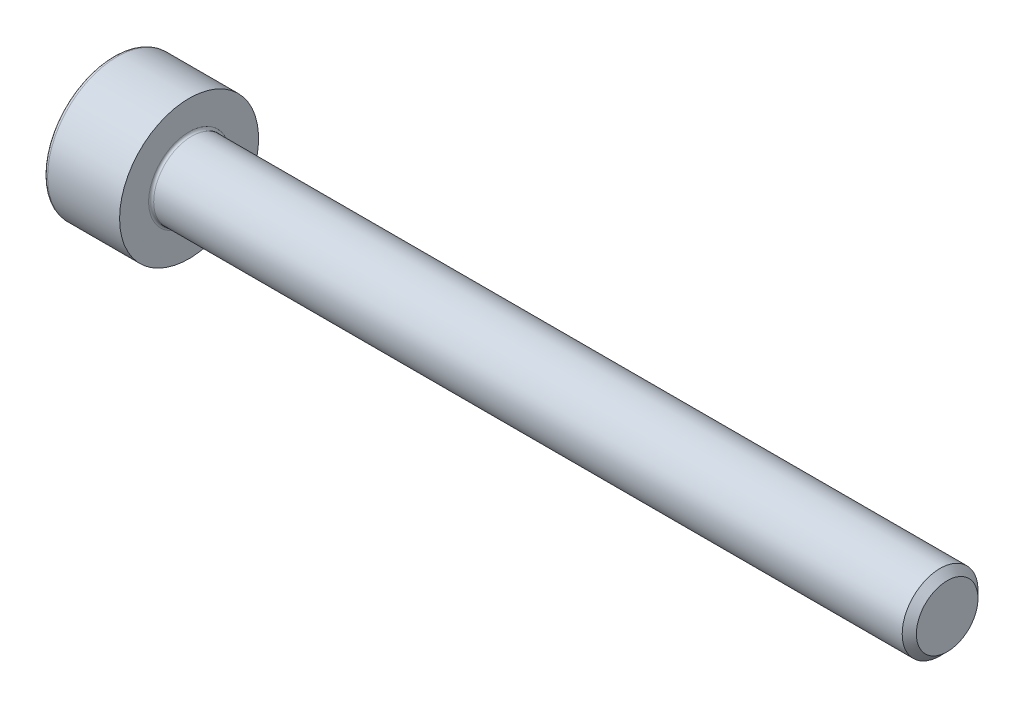
SolidWorks part; units mm, degrees
revolve "Base-Revolve" add sketch "BodySke"
sketch "BodySke" plane through (0, 0, 0) normal (0, 0, 1) x (1, 0, 0)
  line L0 (0, 0) -> (0, 2.75)
  line L1 (0, 2.75) -> (3, 2.75)
  line L2 (3, 2.75) -> (3, 1.5)
  line L3 (3, 1.5) -> (32.7195, 1.5)
  line L4 (33, 1.2195) -> (33, 0)
  line L5 (33, 0) -> (0, 0)
  line L6 (-31.75, 0) -> (127, 0) construction
  line L8 (33, 1.2195) -> (32.7195, 1.5)
  line L10 (33, -1.2195) -> (32.7195, -1.5) construction
  line L11 (3.5, 9.525) -> (3.5, 3.175) construction
  line L12 (15, 9.525) -> (15, 3.175) construction
  line L13 (-27, 9.525) -> (-27, 3.175) construction
  dimension "Body_ch_ang" = 45
  dimension "Advance" = 0.5
  dimension "Thread_length" = 60
cosmetic thread "ThreadCosmetic" [suppressed]
fillet "Fillet1" radius 0.1 1 edges at (3, 0, 1.5)
fillet "Fillet2" radius 0.15 1 edges at (0, 0, 2.75)
ref_plane "Plane1" through (0, 0, 0) normal (0, 0, 1) x (1, 0, 0)
ref_plane "Plane2" through (0, 0, 0) normal (0, 1, 0) x (1, 0, 0)
ref_plane "Plane3" through (0, 0, 0) normal (1, 0, 0) x (0, 0, -1)
other "Configuration Table"
sketch "Sketch2" plane through (0, 0, 0) normal (0, 0, 1) x (1, 0, 0)
  line L0 (0, 1.28) -> (1.3, 1.28)
  line L1 (1.3, 1.28) -> (2.039, 0)
  line L2 (-31.75, 0) -> (127, 0) construction
  line L3 (2.039, 0) -> (0, 0)
  line L4 (0, 0) -> (0, 1.28)
  line L6 (0, 0) -> (47.625, 0) construction
  dimension "D2" = 60
revolve "Hex-PreBroach" cut sketch "Sketch2" angle 360 about L6
sketch "Sketch3" plane through (0, 0, 0) normal (-1, 0, 0) x (0, 0.5, 0.866)
  line L0 (0.739, 1.28) -> (-0.739, 1.28)
  line L1 (-0.739, 1.28) -> (-1.478, 0)
  line L2 (0.739, 1.28) -> (1.478, 0)
  line L3 (0.739, -1.28) -> (1.478, 0)
  line L4 (0.739, -1.28) -> (-0.739, -1.28)
  line L5 (-0.739, -1.28) -> (-1.478, 0)
extrude "Hex" cut sketch "Sketch3" against normal blind 1.3
sketch "ThdSchSke" plane through (0, 0, 0) normal (0, 0, 1) x (1, 0, 0)
  line L0 (15, -1.2195) -> (14.8036, -1.5)
  line L1 (15, -1.2195) -> (15.1964, -1.5)
  line L2 (15.1964, -1.5) -> (15.1964, -1.875)
  line L3 (-3.175, 0) -> (5.1513, 0) construction
  line L4 (0, 2.6) -> (0, -2.6) construction
  line L5 (15.1964, -1.875) -> (14.8036, -1.875)
  line L6 (14.8036, -1.875) -> (14.8036, -1.5)
revolve "ThreadSchematic" [suppressed] cut sketch "ThdSchSke" angle 360 about L3
pattern_linear "ThdSchPat" [suppressed]
equation "\"D2@Sketch3\" = \"Hex_size@Sketch3\" / 2"
equation "\"D1@Sketch3\" = \"Hex_size@Sketch3\" / 2"
equation "\"D1@Sketch2\" = \"Hex_size@Sketch3\" / 2"
equation "\"Thread_minor@ThreadCosmetic\"  =  \"Minor_dia@BodySke\""
equation "\"Depth@Sketch2\" =  \"Key_eng@Hex\""
equation "\"Thread_length@ThreadCosmetic\" = ((sgn( (\"Length@BodySke\" - \"Advance@BodySke\" * 3.0) - \"Thread_nom@BodySke\" )-1)*( (\"Length@BodySke\" - \"Advance@BodySke\" * 3.0) - \"Thread_nom@BodySke\" ))/-2+ \"Thread_nom@BodySke\""
equation "\"Thread_minor@ThdSchSke\" = \"Minor_dia@BodySke\""
equation "\"Diameter@ThdSchSke\" = \"Diameter@BodySke\""
equation "\"Overcut@ThdSchSke\" = \"Diameter@BodySke\" * 1.25"
equation "\"Start@ThdSchSke\" = \"Head_ht@BodySke\" + \"Length@BodySke\" - \"Thread_length@ThreadCosmetic\"  '---Non-countersunk---"
equation "\"Num_threads@ThdSchPat\" = int( \"Thread_length@ThreadCosmetic\" / \"Advance@BodySke\" + 0.999 )  + 1"
equation "\"Advance@ThdSchPat\" = \"Thread_length@ThreadCosmetic\" /  (\"Num_threads@ThdSchPat\" - 1) 'relax it"
equation "\"Num_threads@ThdSchPat\" = \"Num_threads@ThdSchPat\" - sgn( \"Num_threads@ThdSchPat\" - 1) '---chamfered tips only---"
